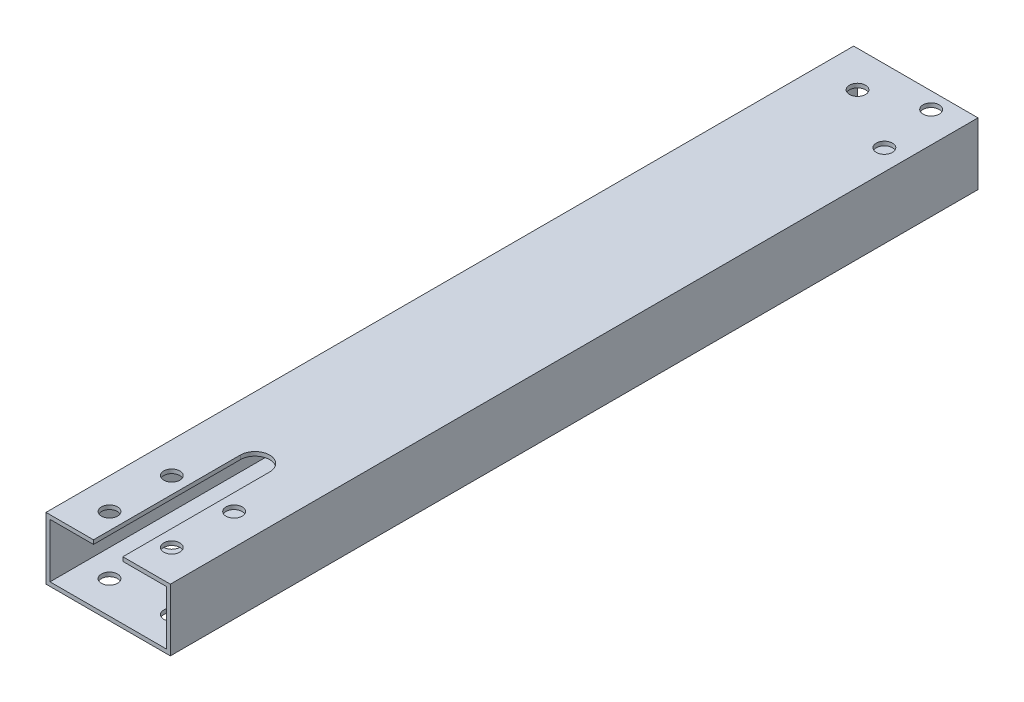
SolidWorks part; units mm, degrees
material "6061-O (SS)"
ref_plane "Front Plane" through (0, 0, 0) normal (0, 0, 1) x (1, 0, 0)
ref_plane "Top Plane" through (0, 0, 0) normal (0, 1, 0) x (1, 0, 0)
ref_plane "Right Plane" through (0, 0, 0) normal (1, 0, 0) x (0, 0, -1)
sketch "Sketch1" plane through (0, 0, 0) normal (0, 0, 1) x (1, 0, 0)
  line L1 (-25.4, 12.7) -> (25.4, 12.7)
  line L2 (-25.4, 12.7) -> (-25.4, -12.7)
  line L3 (-25.4, -12.7) -> (25.4, -12.7)
  line L4 (25.4, 12.7) -> (25.4, -12.7)
  line L5 (-23.749, 11.049) -> (23.749, 11.049)
  line L6 (-23.749, 11.049) -> (-23.749, -11.049)
  line L7 (-23.749, -11.049) -> (23.749, -11.049)
  line L8 (23.749, 11.049) -> (23.749, -11.049)
  point P8 (25.4, 0)
  point P10 (0, 12.7)
  dimension "D1" = 25.4
  dimension "D2" = 50.8
  dimension "D3" = 1.651
  dimension "D4" = 1.651
  dimension "D5" = 1.651
  dimension "D6" = 1.651
extrude "Boss-Extrude1" add sketch "Sketch1" along normal blind 330
sketch "Sketch2" plane through (0, 12.7, 0) normal (0, 1, 0) x (1, 0, 0)
  line L5 (-1.2369, -291.0676) -> (2.0631, -291.0676) construction
  line L8 (25.4, -330) -> (-25.4, -330) construction
  circle A2 centre (-1.2369, -291.0676) radius 3.3
  circle A3 centre (24.1785, -291.2923) radius 3.3
  circle A4 centre (23.9538, -316.7077) radius 3.3
  circle A5 centre (-1.4616, -316.483) radius 3.3
  circle A6 centre (11.4304, -304) radius 18 construction
  dimension "D2" = 26
  dimension "D5" = 4
sketch "Sketch4" plane through (0, 12.7, 0) normal (0, 1, 0) x (1, 0, 0)
  line L0 (-6, -270) -> (-6, -330)
  line L1 (6, -270) -> (6, -330)
  line L2 (-6, -330) -> (6, -330)
  line L5 (25.4, -330) -> (-25.4, -330) construction
  line L6 (25.4, -330) -> (25.4, 0) construction
  arc A0 (6, -270) -> (-6, -270) centre (0, -270) ccw
  point P21 (12.9594, -296.6096)
  dimension "D3" = 6
  dimension "D4" = 60
  dimension "D1" = 0
  dimension "D2" = 25.4
extrude "Cut-Extrude5" cut sketch "Sketch4" against normal up to next
sketch "Sketch8" plane through (0, 12.7, 0) normal (0, 1, 0) x (1, 0, 0)
  line L0 (0, -304) -> (20.6139, -324.6139)
  line L1 (0, -304) -> (-18.2537, -322.2537)
  line L2 (-21.5356, -304) -> (22.2859, -304)
  line L3 (25.4, -330) -> (6, -330) construction
  circle A0 centre (0, -304) radius 18 construction
  circle A3 centre (-12.7279, -316.7279) radius 3.3
  circle A4 centre (12.7279, -316.7279) radius 3.3
  circle A5 centre (12.7279, -291.2721) radius 3.3
  circle A6 centre (-12.7279, -291.2721) radius 3.3
  point P17 (0, -304)
  dimension "D1" = 36
  dimension "D2" = 6.6
  dimension "D3" = 4
  dimension "D6" = 26
  dimension "D4" = 90
  dimension "D5" = 45
extrude "Cut-Extrude6" cut sketch "Sketch8" against normal through all contours L1 A3 | L1 A3 | A6 | A5 | A4
hole_wizard "#00 Clearance Hole1" positions "Sketch9" profile "Sketch10" hole size "#00" standard "ANSI Inch" end condition through all
sketch "Sketch9" plane through (-99.3148, 20.7, -27.3225) normal (0, 1, 0) x (0.866, 0, 0.5)
  point P0 (99.1151, 8.6954)
  point P1 (114.1151, 26.6954)
  point P2 (129.1151, 8.6954)
sketch "Sketch10" plane through (-9.1309, 20.7, 14.7046) normal (1, 0, 0) x (0, 0, 1)
  line L0 (0, 0) -> (0, 33.4)
  line L1 (0, 33.4) -> (3.3, 33.4)
  line L2 (3.3, 33.4) -> (3.3, 0)
  line L3 (3.3, 0) -> (0, 0)
  line L4 (0, -6.35) -> (0, 107.95) construction
  dimension "Thru Hole Dia." = 6.6
  dimension "Thru Hole Depth" = 33.4
